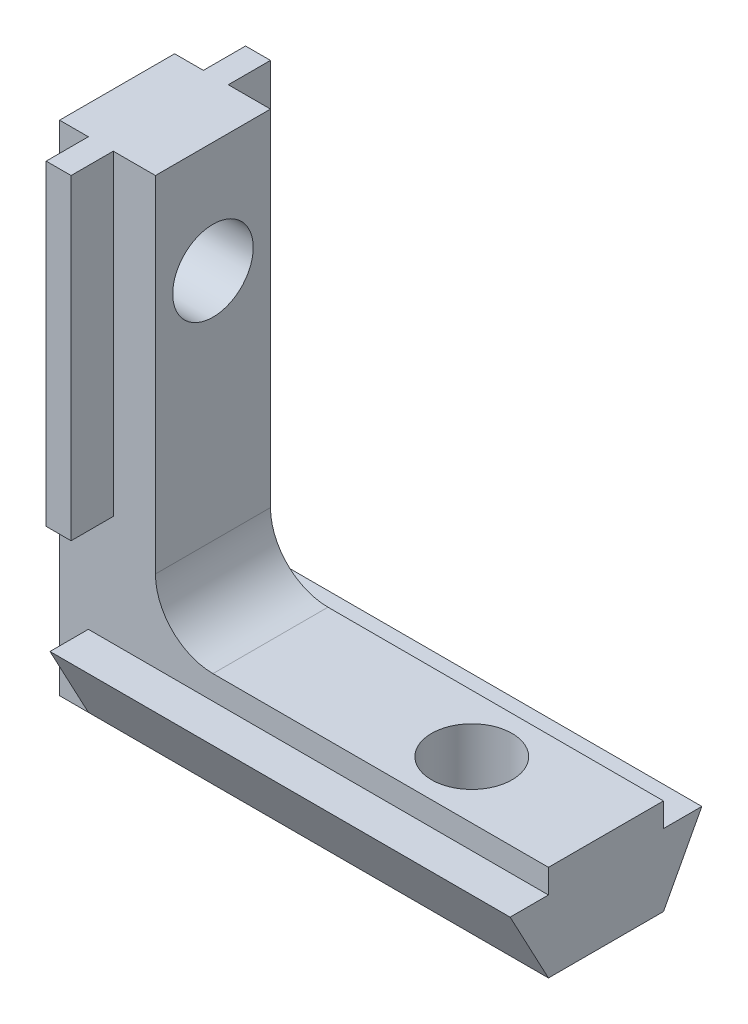
SolidWorks part; units mm, degrees
material "Zinc AC41A Alloy, As Cast"
ref_plane "Front Plane" through (0, 0, 0) normal (0, 0, 1) x (1, 0, 0)
ref_plane "Top Plane" through (0, 0, 0) normal (0, 1, 0) x (1, 0, 0)
ref_plane "Right Plane" through (0, 0, 0) normal (1, 0, 0) x (0, 0, -1)
sketch "Sketch1" plane through (0, 0, 0) normal (0, 0, 1) x (1, 0, 0)
  line L0 (0, 26) -> (0, 0)
  line L1 (0, 0) -> (25.5, 0)
  line L2 (25.5, 0) -> (25.5, 5)
  line L3 (25.5, 5) -> (8, 5)
  line L4 (5, 8) -> (5, 26)
  line L5 (5, 26) -> (0, 26)
  arc A0 (8, 5) -> (5, 8) centre (8, 8) cw
  dimension "D5" = 3
  dimension "D1" = 26
  dimension "D2" = 25.5
  dimension "D3" = 5
  dimension "D4" = 5
extrude "Boss-Extrude1" add sketch "Sketch1" along normal mid plane 6
sketch "Sketch2" plane through (25.5, 0, 0) normal (1, 0, 0) x (0, 0, -1)
  line L0 (-3, 0) -> (-5, 3.75)
  line L1 (-5, 3.75) -> (5, 3.75)
  line L2 (0, 3.75) -> (0, 0) construction
  line L3 (-3, 0) -> (3, 0)
  line L4 (3, 0) -> (5, 3.75)
  line L5 (-3, 5) -> (3, 5) construction
  dimension "D1" = 10
  dimension "D2" = 1.25
extrude "Boss-Extrude2" add sketch "Sketch2" against normal blind 24
sketch "Sketch3" plane through (0, 26, 0) normal (0, 1, 0) x (1, 0, 0)
  line L0 (1.5, 0) -> (0, 0) construction
  line L1 (1.5, 5.2) -> (2.8, 5.2)
  line L2 (1.5, 5.2) -> (1.5, -5.2)
  line L3 (1.5, -5.2) -> (2.8, -5.2)
  line L4 (2.8, 5.2) -> (2.8, -5.2)
  line L5 (0, -3) -> (0, 3) construction
  line L6 (1.5, 5) -> (1.5, 3) construction
  dimension "D1" = 2.8
  dimension "D2" = 10.4
extrude "Boss-Extrude3" add sketch "Sketch3" against normal blind 16.5
hole_wizard "M5x0.8 Tapped Hole1" positions "Sketch5" profile "Sketch4" tap size "M5x0.8" standard "ANSI Metric" end condition through all
sketch "Sketch5" plane through (0, 5, 0) normal (0, 1, 0) x (1, 0, 0)
  line L0 (18.5, 0) -> (25.5, 0) construction
  line L1 (25.5, -3) -> (25.5, 3) construction
  point P0 (18.5, 0)
  dimension "D1" = 7
sketch "Sketch4" plane through (18.5, 5, 0) normal (1, 0, 0) x (0, 0, 1)
  line L0 (0, 0) -> (0, 5)
  line L1 (0, 5) -> (2.1, 5)
  line L2 (2.1, 5) -> (2.1, 0)
  line L5 (2.1, 0) -> (0, 0)
  line L11 (0, -6.35) -> (0, 107.95) construction
  dimension "Thread Major Dia." = 4.2
  dimension "Thru Tap Drill Depth" = 5
hole_wizard "M5x0.8 Tapped Hole2" positions "Sketch7" profile "Sketch6" tap size "M5x0.8" standard "ANSI Metric" end condition through all
sketch "Sketch7" plane through (5, 0, 0) normal (1, 0, 0) x (0, 0, -1)
  line L0 (0, 26) -> (0, 20.2) construction
  line L1 (-3, 26) -> (3, 26) construction
  point P0 (0, 20.2)
  dimension "D1" = 5.8
sketch "Sketch6" plane through (5, 20.2, 0) normal (0, 1, 0) x (0, 0, -1)
  line L0 (0, 0) -> (0, 5)
  line L1 (0, 5) -> (2.1, 5)
  line L2 (2.1, 5) -> (2.1, 0)
  line L5 (2.1, 0) -> (0, 0)
  line L11 (0, -6.35) -> (0, 107.95) construction
  dimension "Thread Major Dia." = 4.2
  dimension "Thru Tap Drill Depth" = 5
